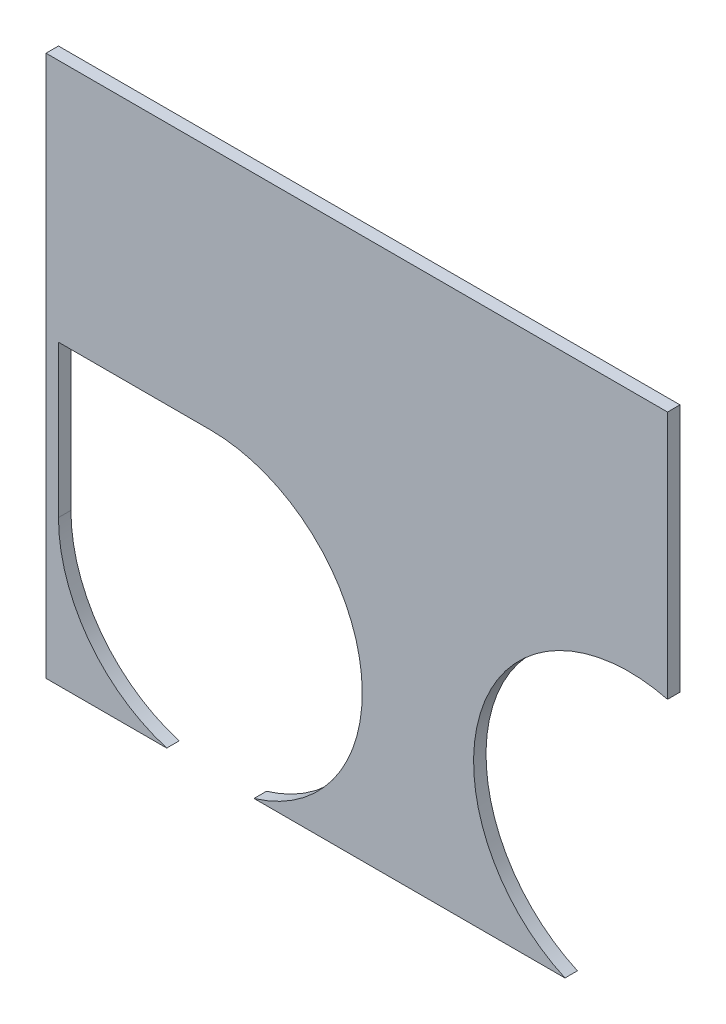
SolidWorks part; units mm, degrees
ref_plane "Front Plane" through (0, 0, 0) normal (0, 0, 1) x (1, 0, 0)
ref_plane "Top Plane" through (0, 0, 0) normal (0, 1, 0) x (1, 0, 0)
ref_plane "Right Plane" through (0, 0, 0) normal (1, 0, 0) x (0, 0, -1)
sketch "Sketch1" plane through (0, 0, 0) normal (0, 0, 1) x (1, 0, 0)
  line L0 (124.8, 0) -> (124.8, -267.4) construction
  line L1 (0, 0) -> (249.6, 0)
  line L2 (0, 0) -> (0, -267.4)
  line L3 (0, -267.4) -> (249.6, -267.4)
  line L4 (249.6, 0) -> (249.6, -267.4)
  line L7 (249.6, -98) -> (249.6, 0) construction
  line L8 (249.6, -267.4) -> (0, -267.4) construction
extrude "Boss-Extrude1" add sketch "Sketch1" along normal blind 5
sketch "Sketch5" plane through (0, 0, 5) normal (0, 0, 1) x (1, 0, 0)
  line L4 (124.8, -267.4) -> (249.6, -267.4)
  line L11 (124.8, -267.4) -> (0, -267.4)
  line L13 (0, -267.4) -> (0, -217.4285)
  line L14 (208.4107, -217.4285) -> (83.5246, -217.4285)
  line L15 (0, -267.4) -> (249.6, -267.4) construction
  line L16 (66, -98) -> (5, -98)
  line L17 (0, -220) -> (0, -267.4) construction
  line L18 (48.4754, -217.4285) -> (0, -217.4285)
  line L19 (0, 0) -> (0, -267.4) construction
  line L20 (135, -217.4285) -> (0, -217.4285) construction
  line L24 (249.6, -267.4) -> (249.6, -99.9255)
  line L25 (5, -159) -> (5, -98)
  line L26 (249.6, -267.4) -> (249.6, 0) construction
  arc A1 (5, -159) -> (48.4754, -217.4285) centre (66, -159) ccw
  arc A3 (234.206, -98) -> (195.5325, -209.598) centre (234.206, -160.5) ccw construction
  arc A4 (83.5246, -217.4285) -> (66, -98) centre (66, -159) ccw
  circle A5 centre (66, -159) radius 60 construction
  arc A6 (249.6, -99.9255) -> (208.4107, -217.4285) centre (234.206, -160.5) ccw
  point P2 (0, 0)
  point P14 (0, 0)
  point P23 (208.4107, -217.4285)
  point P25 (208.4107, -217.4285)
  point P29 (0, 0)
extrude "Cut-Extrude3" cut sketch "Sketch5" against normal through all
